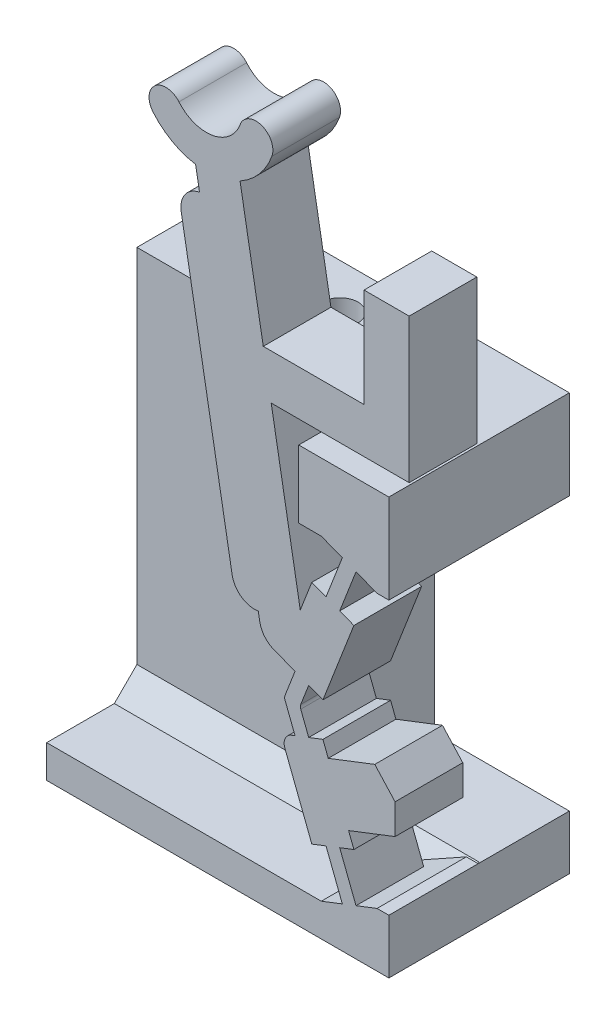
SolidWorks part; units mm, degrees
material "Nylon 6/12"
ref_plane "Front Plane" through (0, 0, 0) normal (0, 0, 1) x (1, 0, 0)
ref_plane "Top Plane" through (0, 0, 0) normal (0, 1, 0) x (1, 0, 0)
ref_plane "Right Plane" through (0, 0, 0) normal (1, 0, 0) x (0, 0, -1)
sketch "Sketch-SkeletonConfigUp" plane through (0, 0, 0) normal (0, 0, 1) x (1, 0, 0)
  line L0 (0, 0) -> (0, -50000) construction
  line L1 (-1.4217, 8.457) -> (-1.4217, 0) construction
  line L3 (0.7468, 14.0514) -> (-1.4217, 8.457) construction
  line L4 (-1.4217, 8.457) -> (0.7468, 2.8626) construction
  line L5 (0.7468, 14.0514) -> (2.1074, 19.3343) construction
  line L6 (-1.4217, 8.457) -> (-5.2203, 30) construction
  line L9 (0.7468, 14.0514) -> (0.7468, 2.8626) construction
  line L10 (0.7468, 2.8626) -> (0.7468, 0) construction
  line L11 (0, 0) -> (0.7468, 0) construction
  line L12 (0.7468, 0) -> (0, 0) construction
  dimension "D7" = 5.4552
  dimension "D10" = 6.745
  dimension "D3" = 2.1685
  dimension "D9" = 10
  dimension "D13" = 11.1888
  dimension "D14" = 30
  dimension "D5" = 10
  dimension "D2" = 21.8753
  dimension "D4" = 6
sketch "Sketch-SkeletonConfigDown" plane through (0, 0, 0) normal (0, 0, 1) x (1, 0, 0)
  line L0 (0, 0) -> (0, -50000) construction
  line L1 (0.7468, 14.0514) -> (0.7468, 2.8626) construction
  line L2 (5.9945, 14.5439) -> (0.7468, 14.0514) construction
  line L3 (0.7468, 14.0514) -> (2.9153, 8.457) construction
  line L4 (2.9153, 8.457) -> (0.7468, 2.8626) construction
  line L5 (0.7468, 14.0514) -> (-1.8086, 18.8711) construction
  line L6 (2.9153, 8.457) -> (-14.411, 21.8109) construction
  line L7 (0.7468, 2.8626) -> (5.9945, 14.5439) construction
  line L8 (-387.6937, -861.8102) -> (5.9945, 14.5439) construction
  line L10 (-1.4217, 8.457) -> (0.7468, 2.8626) construction
  line L11 (0.7468, 14.0514) -> (-1.4217, 8.457) construction
  line L12 (-1.4217, 8.457) -> (-5.2203, 30) construction
  line L13 (0.7468, 14.0514) -> (2.1074, 19.3343) construction
  dimension "D10" = 6.745
  dimension "D4" = 5.2707
  dimension "D5" = 119.553
  dimension "D2" = 52.378
  dimension "D3" = 31.19
ref_plane "Plane-Cam Base" through (3.8672, 0, 0) normal (1, 0, 0) x (0, 0, -1)
ref_plane "Plane-Down-to-Up Derailleur Clearance" through (1.3672, 0, 0) normal (1, 0, 0) x (0, 0, -1)
ref_plane "Plane-Cam Cavity Roof" through (-0.1328, 0, 0) normal (1, 0, 0) x (0, 0, -1)
sketch "Sketch-SwitchBossUp" plane through (0, 0, 0) normal (0, 0, 1) x (1, 0, 0)
  line L8 (-5.6979, 26.9497) -> (-5.5242, 25.9649)
  line L9 (-1.4217, 8.457) -> (-5.2203, 30) construction
  line L15 (-1.291, 7.2207) -> (-0.685, 7.4556) construction
  line L16 (-1.4217, 8.457) -> (0.7468, 2.8626) construction
  line L19 (0.0824, 13.2365) -> (0.6884, 13.0016) construction
  line L22 (0.8052, 15.1013) -> (1.4113, 14.8664) construction
  line L23 (-1.291, 9.6934) -> (-1.9204, 9.9373)
  line L32 (1.0498, 2.9801) -> (0.4438, 2.7452) construction
  line L40 (-1.7703, 8.457) -> (-1.0732, 8.457) construction
  line L66 (-5.2203, 27.8193) -> (-5.2203, 50027.8193) construction
  line L74 (-4.078, 12.0039) -> (-6.3354, 24.8064)
  line L81 (2.3437, 2.4091) -> (2.8672, 2.4091)
  line L82 (-5.6111, 26.4573) -> (-3.6415, 26.8046) construction
  line L88 (-0.1116, 18.4627) -> (2.8672, 18.4627)
  line L92 (0.6311, 5.928) -> (-1.2337, 5.2052) construction
  line L95 (-2.3469, 19.4627) -> (3.7672, 19.4627)
  line L96 (2.8672, 14.505) -> (2.8672, 18.4627)
  line L97 (3.7672, 19.4627) -> (3.7672, 25.8576)
  line L101 (-0.988, 7.3382) -> (-1.4217, 8.457) construction
  line L103 (-5.2203, 30) -> (-3.0238, 29.2005) construction
  line L107 (-1.291, 9.6934) -> (-0.685, 9.4585) construction
  line L109 (-5.2203, 30) -> (-7.011, 28.4975) construction
  line L114 (-0.0556, 7.6996) -> (-0.685, 7.4556)
  line L117 (2.8672, 0) -> (-0.1272, 0)
  line L121 (0.7468, 0) -> (0, 0) construction
  line L122 (0.8052, 1.8128) -> (-0.1272, 1.4513)
  line L123 (1.4113, 2.0477) -> (2.3437, 2.4091)
  line L125 (2.8672, 2.4091) -> (2.8672, 0)
  line L127 (-0.685, 9.4585) -> (-0.0556, 9.2145)
  line L133 (0.4438, 14.1689) -> (1.0498, 13.934) construction
  line L134 (-0.0556, 9.2145) -> (1.3178, 12.7576)
  line L135 (0.6884, 13.0016) -> (1.3178, 12.7576)
  line L142 (-0.1272, 1.4513) -> (-0.1272, 0)
  line L151 (0.0824, 13.2365) -> (-0.547, 13.4805)
  line L152 (0.8052, 15.1013) -> (0.0824, 13.2365)
  line L153 (1.4113, 14.8664) -> (0.6884, 13.0016)
  line L169 (0.0824, 3.6776) -> (0.8052, 1.8128)
  line L170 (1.4113, 2.0477) -> (0.6884, 3.9125)
  line L177 (0.6884, 3.9125) -> (0.0824, 3.6776) construction
  line L184 (-0.547, 13.4805) -> (-1.0591, 12.1594)
  line L191 (-1.291, 7.2207) -> (-1.9204, 6.9767)
  line L197 (3.7672, 25.8576) -> (1.7672, 25.8576)
  line L205 (1.7672, 25.8576) -> (1.7672, 21.4627)
  line L207 (12.0045, 16.6962) -> (12.0045, 16.6883) construction
  line L218 (0.6884, 3.9125) -> (1.3178, 4.1564)
  line L225 (-1.0591, 12.1594) -> (-2.3469, 19.4627)
  line L235 (-5.5242, 25.9649) -> (-2.7552, 10.2609) construction
  line L236 (-1.9204, 6.9767) -> (-0.547, 3.4336)
  line L237 (-2.7552, 10.2609) -> (-2.9195, 11.1927)
  line L241 (-1.4217, 8.457) -> (-0.988, 9.5759) construction
  line L242 (1.7672, 21.4627) -> (-2.6996, 21.4627)
  line L243 (-0.685, 7.4556) -> (-1.0381, 8.3667)
  line L244 (-1.0381, 8.5474) -> (-0.685, 9.4585)
  line L245 (-1.291, 7.2207) -> (-1.7353, 8.3667)
  line L246 (-1.7353, 8.5474) -> (-1.291, 9.6934)
  line L247 (-0.0556, 7.6996) -> (0.1811, 7.089)
  line L248 (0.8052, 1.8128) -> (1.4113, 2.0477) construction
  line L249 (0.0824, 3.6776) -> (-0.547, 3.4336)
  line L250 (-1.9204, 9.9373) -> (-0.547, 13.4805) construction
  line L251 (0.7468, 14.0514) -> (-1.4217, 8.457) construction
  line L252 (-1.2699, 11.6157) -> (0.5949, 10.8928) construction
  line L253 (-2.3469, 19.4627) -> (-2.6996, 21.4627) construction
  line L254 (-1.9204, 9.9373) -> (-2.7552, 10.2609)
  line L255 (0.8052, 15.1013) -> (-0.1272, 15.4627)
  line L256 (1.4113, 14.8664) -> (2.3437, 14.505)
  line L257 (2.3437, 14.505) -> (2.8672, 14.505)
  line L258 (-2.6996, 21.4627) -> (-3.7283, 27.297)
  line L259 (3.8672, -55) -> (3.8672, 55) construction
  line L260 (0.1811, 7.089) -> (2.2431, 7.8883)
  line L261 (3.1433, 6.9018) -> (3.1433, 5.5663)
  line L262 (3.1433, 5.5663) -> (1.0811, 4.767)
  line L263 (0.6311, 5.928) -> (3.1433, 6.9018) construction
  line L264 (1.0811, 4.767) -> (0.6311, 5.928) construction
  line L265 (1.0811, 4.767) -> (1.3178, 4.1564)
  line L266 (0.6311, 5.928) -> (0.1811, 7.089) construction
  line L267 (0.1811, 7.089) -> (0.6311, 5.928) construction
  line L268 (0.6311, 5.928) -> (1.0811, 4.767) construction
  line L269 (0.1811, 7.089) -> (0.6311, 5.928) construction
  line L270 (0.6311, 5.928) -> (1.0811, 4.767) construction
  line L271 (3.1433, 6.9018) -> (2.2431, 7.8883)
  line L272 (1.8311, 5.6598) -> (3.8672, 4.8706) construction
  line L273 (2.9153, 8.457) -> (0.7468, 2.8626) construction
  line L274 (-0.3013, 5.5666) -> (2.2431, 7.8883) construction
  line L275 (-0.3013, 5.5666) -> (3.8672, 5.5666) construction
  line L276 (-0.1272, 15.4627) -> (-1.1272, 15.4627)
  line L277 (-1.1272, 15.4627) -> (-1.1272, 18.4627)
  line L278 (-1.1272, 18.4627) -> (-0.1116, 18.4627)
  arc A0 (-3.7283, 27.297) -> (-2.319, 28.944) centre (-5.2203, 30) ccw
  arc A1 (-5.6979, 26.9497) -> (-7.5855, 28.0154) centre (-5.2203, 30) cw
  arc A2 (-7.5855, 28.0154) -> (-6.4364, 28.9796) centre (-7.011, 28.4975) cw
  arc A3 (-2.319, 28.944) -> (-3.7286, 29.457) centre (-3.0238, 29.2005) ccw
  arc A4 (-6.4364, 28.9796) -> (-3.7286, 29.457) centre (-5.2203, 30) ccw
  arc A19 (-6.3354, 24.8064) -> (-5.5242, 25.9649) centre (-5.3506, 24.98) cw
  circle A28 centre (-5.2203, 30) radius 2.3375 construction
  arc A30 (-4.078, 12.0039) -> (-2.9195, 11.1927) centre (-3.0932, 12.1775) ccw
  arc A31 (-1.0381, 8.3667) -> (-1.0381, 8.5474) centre (-0.805, 8.457) cw
  arc A32 (-1.7353, 8.3667) -> (-1.7353, 8.5474) centre (-1.5022, 8.457) cw
  point P5 (-4.6263, 26.6309)
  point P6 (-0.3013, 5.5666)
  point P45 (-0.3375, 11.2542)
  point P66 (4.5811, 6.2164)
  point P165 (0.7468, 14.0514)
  dimension "D23" = 1.5875
  dimension "D24" = 0.75
  dimension "D21" = 0.25
  dimension "D8" = 0.65
  dimension "D27" = 0.65
  dimension "D26" = 2
  dimension "D3" = 1.2
  dimension "D5" = 1.2
  dimension "D16" = 2
  dimension "D28" = 2
  dimension "D29" = 2
  dimension "D30" = 1
  dimension "D31" = 15
  dimension "D4" = 1.4169
  dimension "D6" = 0.65
  dimension "D7" = 2
  dimension "D11" = 1
  dimension "D10" = 1
  dimension "D9" = 0
  dimension "D12" = 60
  dimension "D13" = 60
  dimension "D14" = 2
  dimension "D15" = 1
  dimension "D17" = 2
  dimension "D19" = 0.1
  dimension "D22" = 42.38
  dimension "D18" = 3
  dimension "D25" = 1
  dimension "D32" = 1
  dimension "D20" = 1
extrude "Boss-Switch Body" add sketch "Sketch-SwitchBossUp" along normal blind 3
sketch "Sketch1" plane through (0, 0, 0) normal (0, 0, -1) x (-1, 0, 0)
  line L0 (-2.8672, 2.4091) -> (0.1272, 2.4091)
  line L1 (-2.8672, 0) -> (0.1272, 0)
  line L2 (-2.8672, 0) -> (-2.8672, 2.4091)
  line L4 (0.1272, 0) -> (0.1272, 2.4091)
  line L5 (1.1272, 14.505) -> (-2.8672, 14.505)
  line L10 (-2.8672, 14.505) -> (-2.8672, 18.4627)
  line L12 (-2.8672, 18.4627) -> (1.1272, 18.4627)
  line L14 (1.1272, 18.4627) -> (1.1272, 14.505)
  line L20 (-2.3437, 2.4091) -> (-2.8672, 2.4091) construction
  line L22 (-2.8672, 2.4091) -> (-2.3437, 2.4091) construction
  line L31 (0.1272, 0) -> (-2.8672, 0) construction
  line L32 (0.1272, 1.4513) -> (0.1272, 0) construction
extrude "Boss-Flange Width" add sketch "Sketch1" along normal blind 5
ref_plane "Plane-Sta2Sit Groove" through (-5.2203, 0, 0) normal (1, 0, 0) x (0, 0, -1)
ref_plane "Plane-Cam Outer Surface" through (-17.3003, 0, 0) normal (1, 0, 0) x (0, 0, -1)
ref_plane "Plane-FlangeTop" through (-12.3003, 0, 0) normal (1, 0, 0) x (0, 0, -1)
sketch "Sketch2" plane through (-12.3003, 0, 0) normal (1, 0, 0) x (0, 0, -1)
  line L0 (5, 18.4627) -> (-3, 18.4627) construction
  line L1 (5, 14.505) -> (1, 14.505)
  line L2 (5, 14.505) -> (5, 18.4627)
  line L3 (5, 18.4627) -> (1, 18.4627)
  line L4 (1, 14.505) -> (1, 18.4627)
  line L5 (5, 14.505) -> (-3, 14.505) construction
  line L11 (5, 1.4513) -> (-3, 1.4513)
  line L12 (5, 1.4513) -> (5, 0)
  line L13 (5, 0) -> (-3, 0)
  line L14 (-3, 1.4513) -> (-3, 0)
  line L15 (0, 8.457) -> (0, 30) construction
  line L16 (-3, 1.4513) -> (-3, 0) construction
  line L17 (5, 2.4091) -> (5, 0) construction
  line L19 (-3, 1.4513) -> (0, 1.4513) construction
  dimension "D1" = 1
extrude "Boss-Flange Height" add sketch "Sketch2" along normal up to surface (12.1731 mm away) up to face at (-0.1272, 1.2868, -0.6667)
sketch "Sketch17" plane through (0, 1.4513, 0) normal (0, -1, 0) x (1, 0, 0)
  line L0 (2.8672, -5) -> (-12.3003, -5)
  line L1 (2.8672, -5) -> (-12.3003, -5) construction
  line L2 (-12.3003, -5) -> (-12.3003, -1)
  line L3 (-12.3003, -1) -> (2.8672, -1)
  line L4 (2.8672, -1) -> (2.8672, -5)
  line L5 (-12.3003, -1) -> (-12.3003, -5) construction
  line L7 (-1.1272, -1) -> (-12.3003, -1) construction
extrude "Boss-Flange Support" add sketch "Sketch17" against normal up to surface (13.0536 mm away) up to face at (-1.4588, 14.505, -0.6)
sketch "Sketch27" plane through (0, 0, 0) normal (0, 0, 1) x (1, 0, 0)
  line L1 (-0.1272, 15.4627) -> (2.3437, 14.505)
  line L2 (2.3437, 14.505) -> (-1.1272, 14.505)
  line L3 (-1.1272, 14.505) -> (-1.1272, 15.4627)
  line L4 (-1.1272, 15.4627) -> (-0.1272, 15.4627)
  line L6 (-1.1272, 14.505) -> (2.8672, 14.505) construction
  line L7 (2.3437, 14.505) -> (1.2712, 14.505) construction
  line L8 (2.3437, 2.4091) -> (-0.1272, 2.4091)
  line L9 (-0.1272, 2.4091) -> (-0.1272, 1.4513)
  line L10 (-0.1272, 1.4513) -> (2.3437, 2.4091)
extrude "Cut-Wall Gap" cut sketch "Sketch27" against normal up to surface (1 mm away) up to face at (-2.6719, 9.207, -1)
ref_plane "Plane-Tap Depth" through (0, 13.4627, 0) normal (0, 1, 0) x (1, 0, 0)
sketch "Sketch-HolePositions" plane through (0, 0, 0) normal (0, -1, 0) x (1, 0, 0)
  line L0 (-12.3003, -3) -> (2.8672, -3) construction
  line L1 (2.8672, -5) -> (-12.3003, -5) construction
  line L2 (2.8672, -5) -> (2.8672, 3) construction
  line L4 (-12.3003, -22.2167) -> (-12.3003, 22.2167) construction
  point P6 (-9.3003, -3)
  point P7 (-5.3003, -3)
  dimension "D1" = 3
  dimension "D2" = 4
  dimension "D3" = 2
sketch "Sketch6" plane through (0, 0, 0) normal (0, -1, 0) x (-1, 0, 0)
  point P0 (9.3003, 3)
  point P3 (5.3003, 3)
hole_wizard "Tap Drill for M2x0.4 Tap1" positions "Sketch6" profile "Sketch5" hole size "M2x0.4" standard "ANSI Metric" end condition through all
sketch "Sketch5" plane through (-9.3003, 0, -3) normal (1, 0, 0) x (0, 0, -1)
  line L0 (0, 0) -> (0, 29.9505)
  line L1 (0, 29.9505) -> (0.8, 29.9505)
  line L2 (0.8, 29.9505) -> (0.8, 0)
  line L5 (0.8, 0) -> (0, 0)
  line L11 (0, -6.35) -> (0, 107.95) construction
  dimension "Thru Hole Dia." = 1.6
  dimension "Thru Hole Depth" = 29.9505
sketch "Sketch9" plane through (0, 0, 0) normal (0, -1, 0) x (1, 0, 0)
  point P0 (-9.3003, -3)
  point P3 (-5.3003, -3)
hole_wizard "M2 Clearance Hole2" positions "Sketch9" profile "Sketch8" hole size "M2" standard "ANSI Metric"
sketch "Sketch8" plane through (-9.3003, 0, -3) normal (1, 0, 0) x (0, 0, -1)
  line L0 (0, 0) -> (0, 14.1838)
  line L1 (0, 14.1838) -> (1.2, 13.4627)
  line L2 (1.2, 13.4627) -> (1.2, 0)
  line L5 (1.2, 0) -> (0, 0)
  line L10 (0, 14.1838) -> (-1.2, 13.4627) construction
  line L11 (0, -6.35) -> (0, 107.95) construction
  dimension "Hole Dia." = 2.4
  dimension "Hole Depth" = 13.4627
  dimension "Drill Angle" = 118
sketch "Sketch-Measurements for Derailleur Ramps" [suppressed] plane through (0, 0, 0) normal (0, 0, 1) x (1, 0, 0)
  line L0 (2.8784, 16.9852) -> (4.2265, 19.8331)
  line L1 (3.5524, 18.4092) -> (3.0492, 18.6474)
  line L2 (1.9779, 11.0613) -> (4.4465, 28.5428) construction
  line L3 (3.0492, 18.6474) -> (-4.0642, 13.8428)
  line L4 (7.1843, 11.0614) -> (-9.9544, 15.2993) construction
  line L5 (3.0492, 18.6474) -> (2.1536, 12.3053)
  line L6 (2.1536, 12.3053) -> (-4.0642, 13.8428)
  line L7 (-0.5075, 16.2451) -> (-0.5075, 18.6474)
  line L8 (-0.5075, 18.6474) -> (3.0492, 18.6474)
  line L9 (7.1843, 11.0614) -> (1.9779, 11.0613)
  line L10 (5.8827, 8.6389) -> (3.2795, 8.6389)
  line L12 (7.1843, 11.0614) -> (4.5811, 6.2164) construction
  line L13 (4.5811, 8.6389) -> (4.5811, 8.7912)
  line L14 (4.5811, 6.2164) -> (5.8827, 8.6389)
  line L15 (1.9779, 11.0613) -> (4.5811, 6.2164) construction
  line L16 (3.2795, 8.6389) -> (4.5811, 6.2164)
  line L17 (5.8827, 8.6389) -> (5.8827, 8.7912)
  dimension "D1" = 3.5567
  dimension "D2" = 1.3016
sketch "Sketch12" [suppressed] plane through (0, 23.1883, 0) normal (0, 1, 0) x (1, 0, 0)
  line L0 (10.0045, 0) -> (12.0045, -3)
  line L1 (12.0045, -3) -> (12.0045, 0)
  line L2 (12.0045, 0) -> (10.0045, 0)
extrude "Cut-Up-to-Down Cantilever Slope" [suppressed] cut sketch "Sketch12" against normal up to next
ref_plane "Plane1" [suppressed] through (0, 6.9404, 0) normal (0, 1, 0) x (1, 0, 0)
sketch "Sketch-Derailleur Location" [suppressed] plane through (0, 6.9404, 0) normal (0, 1, 0) x (1, 0, 0)
  line L0 (12.9465, 0) -> (12.9465, -3)
  line L1 (4.2399, -3) -> (3.2603, -3) construction
  line L2 (-119237.4187, 0) -> (9.8143, 0) construction
  point P0 (12.9465, 0)
  point P8 (12.9465, -1.5)
ref_plane "Plane-Cantilever Cut" [suppressed] through (7.0848, 8.5204, -1.9058) normal (-0.6301, -0.7578, 0.1695) x (-0.7765, 0.6151, -0.1368)
sketch "Sketch14" [suppressed] plane through (7.0848, 8.5204, -1.9058) normal (-0.6301, -0.7578, 0.1695) x (-0.7765, 0.6151, -0.1368)
  line L0 (2.3023, -1.6911) -> (-0.3551, -1.6911)
  line L2 (2.3023, -4.3362) -> (2.3023, -1.6911)
  line L3 (-0.3551, -1.6911) -> (-0.3551, -4.4608)
  line L5 (-0.3551, -4.4608) -> (1.0087, -5.0843)
  line L6 (1.0087, -5.0843) -> (2.3023, -4.3362)
extrude "Cut-Down-to-Up Cantilever Slope" [suppressed] cut sketch "Sketch14" against normal up to next
ref_plane "Plane-Symmetry Plane" through (0, 0, 1.5) normal (0, 0, 1) x (1, 0, 0)
sketch "Sketch-Cable Center Point" plane through (0, 0, 1.5) normal (0, 0, 1) x (1, 0, 0)
  line L0 (-5.2203, 30) -> (-5.0825, 29.2183)
  line L1 (-1.4217, 8.457) -> (-5.2203, 30) construction
  point P0 (-5.2203, 30)
  dimension "D1" = 0.7937
sketch "Sketch28" plane through (0, 0, -1) normal (0, 0, 1) x (1, 0, 0)
  line L0 (2.8672, 14.505) -> (2.8672, 2.4091)
  line L1 (2.3437, 2.4091) -> (2.8672, 2.4091) construction
  line L2 (2.8672, 14.505) -> (-3.1003, 14.505)
  line L3 (-3.1003, 14.505) -> (-3.1003, 2.4091)
  line L4 (-3.1003, 2.4091) -> (2.8672, 2.4091)
  line L6 (-6.5003, 13.4627) -> (-4.1003, 13.4627) construction
  line L7 (-6.5003, 13.4627) -> (-4.1003, 13.4627) construction
  dimension "D1" = 1
chamfer "Chamfer-Flange Support" [suppressed] distance 1.5 angle 45
chamfer "Chamfer-Flange Support 3" distance 1 angle 45 1 edges at (-6.2138, 1.4513, -1)
fillet "Fillet1" radius 1 1 edges at (-2.7552, 10.2609, 1.5)
fillet "Fillet2" radius 0.5 1 edges at (-1.9204, 6.9767, 1.5)
extrude "Cut-Print Support Clearance" cut sketch "Sketch28" against normal through all
equation "\"axle-diameter\"=2"
equation "\"switch-thickness\"=12"
equation "\"base-width\"=4.0"
equation "\"axle-bushing-radius\"=3"
equation "\"clearance\"= 0.25"
equation "\"arm-width\"=1.5"
equation "\"min-diameter\"=70"
equation "\"alpha\"=143.6120"
equation "\"gamma\"=119.5526"
equation "\"delta\"=145.9637"
equation "\"epsilon\"=6.7452"
equation "\"l_AB\"=8.8212"
equation "\"l_AC\"=4.4914"
equation "\"l_BD\"=5.2707"
equation "\"l_CD\"=3.8848"
equation "\"l_CE\"=10.9181"
equation "\"l_DF\"=5.4552"
equation "\"l_OA\"=7.7221"
equation "\"D7@Sketch-SkeletonConfigUp\" = \"l_DF\""
equation "\"D_groove\"=3.175"
equation "\"D5@Sketch-SkeletonConfigDown\" = \"gamma\""
equation "\"D4@Sketch-SkeletonConfigDown\" = \"l_BD\""
equation "\"hinge_length\"=1.5"
equation "\"hinge_depth\"=0.25"
equation "\"D10@Sketch-SkeletonConfigUp\"=\"epsilon\""
equation "\"D10@Sketch-SkeletonConfigDown\"=\"epsilon\""
equation "\"EE_dx\"=8.9056"
equation "\"EE_dy\"=8.1898"
equation "\"r_groove\"=\"D_groove\"/2"
equation "\"t_wall\"=25.4/16"
equation "\"width_lower\"=\"D_groove\"+\"t_wall\""
equation "\"cable_to_bottom\"=30.6257"
equation "\"switch_EE-up_base_dy\"=24"
equation "\"switch_EE-down_base_dy\"=16"
equation "\"D_axle\"=25.4/8"
equation "\"D_up_to_down\"=16"
equation "\"D_down_to_up\"=25"
equation "\"t_cam_base\"=7.5"
equation "\"D23@Sketch-SwitchBossUp\"=\"D_groove\"/2"
equation "\"D1@Sketch-Cable Center Point\"=\"D_groove\"/4"
